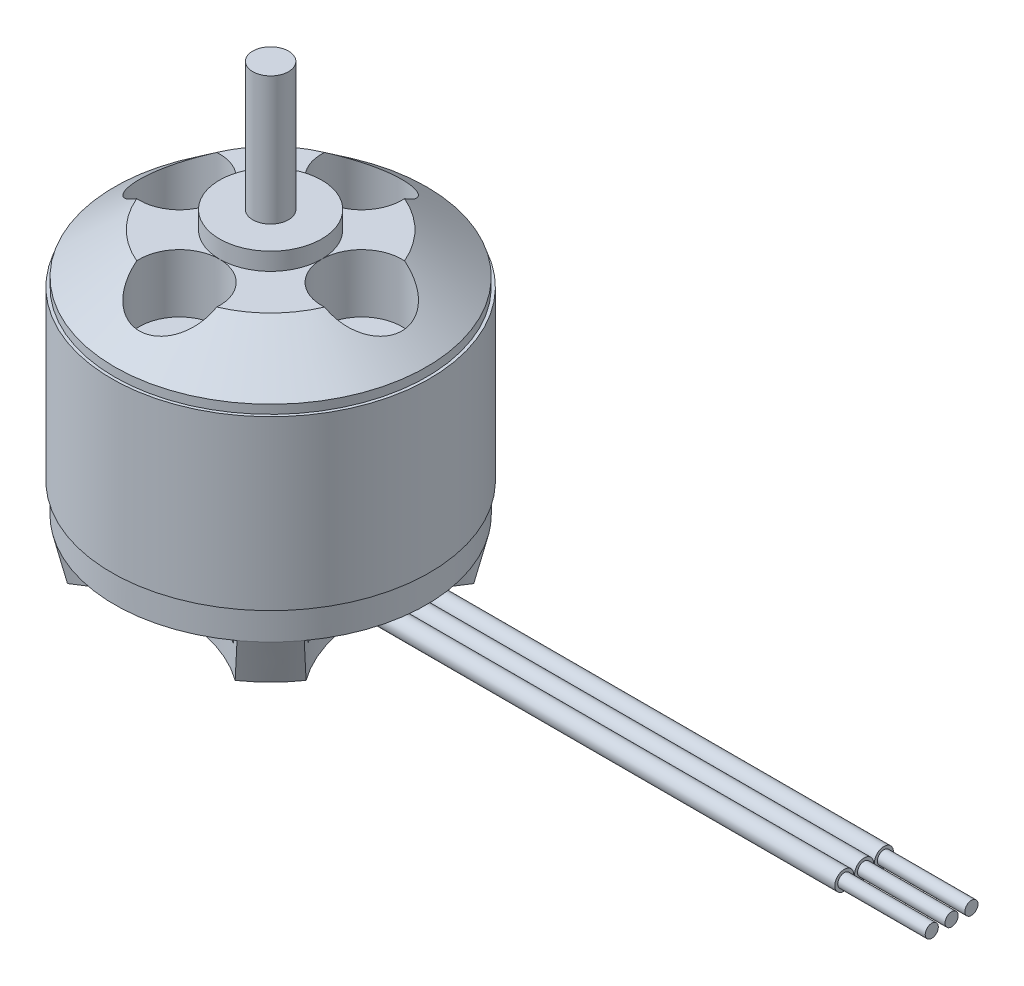
SolidWorks part; units mm, degrees
material "Plain Carbon Steel"
ref_plane "Front" through (0, 0, 0) normal (0, 0, 1) x (1, 0, 0)
ref_plane "Top" through (0, 0, 0) normal (0, 1, 0) x (1, 0, 0)
ref_plane "Right" through (0, 0, 0) normal (1, 0, 0) x (0, 0, -1)
sketch "Sketch1" plane through (0, 0, 0) normal (0, 0, 1) x (1, 0, 0)
  line L0 (0, 11.176) -> (1.5558, 11.176)
  line L1 (0, -50) -> (0, 50) construction
  line L2 (1.5558, 11.176) -> (1.5558, 0)
  line L3 (50, 0) -> (-50, 0) construction
  line L4 (1.5558, 0) -> (4.445, 0)
  line L5 (4.445, 0) -> (4.445, -1.524)
  line L6 (4.445, -1.524) -> (8.89, -1.524)
  line L7 (8.89, -1.524) -> (13.589, -5.08)
  line L8 (13.589, -5.08) -> (13.589, -5.842)
  line L9 (13.589, -5.842) -> (13.843, -5.842)
  line L10 (13.843, -5.842) -> (13.843, -20.4724)
  line L11 (13.589, -20.4724) -> (13.589, -23.0124)
  line L12 (13.589, -23.0124) -> (12.7, -26.67)
  line L13 (12.7, -26.67) -> (3.81, -26.67)
  line L14 (3.81, -26.67) -> (3.81, -26.924)
  line L15 (3.81, -26.924) -> (1.5558, -26.924)
  line L16 (1.5558, -26.924) -> (1.5558, -28.956)
  line L17 (1.5558, -28.956) -> (0, -28.956)
  line L18 (0, -28.956) -> (0, 11.176)
  line L19 (13.589, -20.4724) -> (13.843, -20.4724)
  dimension "D1" = 13.843
  dimension "D2" = 1.5557
  dimension "D3" = 11.176
  dimension "D4" = 4.445
  dimension "D5" = 1.524
  dimension "D6" = 8.89
  dimension "D7" = 4.318
  dimension "D8" = 0.762
  dimension "D9" = 0.254
  dimension "D10" = 14.6304
  dimension "D11" = 2.54
  dimension "D12" = 25.146
  dimension "D13" = 12.7
  dimension "D14" = 3.81
  dimension "D15" = 0.254
  dimension "D16" = 40.132
revolve "Revolve1" add sketch "Sketch1" angle 360 about L18
sketch "Sketch2" plane through (0, -1.524, 0) normal (0, 1, 0) x (1, 0, 0)
  circle A0 centre (0, 7.9375) radius 3.4925
  circle A1 centre (7.9375, 0) radius 3.4925
  circle A2 centre (0, -7.9375) radius 3.4925
  circle A3 centre (-7.9375, 0) radius 3.4925
  circle A5 centre (0, 0) radius 4.445 construction
  circle A7 centre (0, 0) radius 4.445 construction
  dimension "D2" = 6.985
extrude "Cut-Extrude1" cut sketch "Sketch2" against normal blind 5.08
sketch "Sketch3" plane through (0, -26.67, 0) normal (0, -1, 0) x (1, 0, 0)
  line L1 (-7.3025, 10.3905) -> (7.3025, 10.3905) construction
  circle A0 centre (0, 20.4866) radius 12.4602
  circle A1 centre (-20.4866, 0) radius 12.4602
  circle A2 centre (0, -20.4866) radius 12.4602
  circle A3 centre (20.4866, 0) radius 12.4602
  circle A4 centre (0, 0) radius 8.0264 construction
  circle A5 centre (0, 0) radius 12.7 construction
  dimension "D1" = 16.0528
  dimension "D2" = 14.605
extrude "Cut-Extrude2" cut sketch "Sketch3" against normal offset from surface (3.6576 mm away) 2.54 up to face at (0, -20.4724, -13.843)
sketch "Sketch4" plane through (0, -23.0124, 0) normal (0, -1, 0) x (1, 0, 0)
  circle A0 centre (0, 0) radius 12.1158
  arc A2 (8.0324, 10.9609) -> (-8.0324, 10.9609) centre (0, 0) ccw construction
  dimension "D1" = 1.4732
extrude "Cut-Extrude3" cut sketch "Sketch4" against normal blind 2.54 and the other way blind 1.27
hole_wizard "#4-40 Tapped Hole1" positions "Sketch7" profile "Sketch6" tap size "#4-40" standard "ANSI Inch"
sketch "Sketch7" plane through (0, -26.67, 0) normal (0, -1, 0) x (-1, 0, 0)
  line L0 (6.6723, 6.6723) -> (-6.6723, -6.6723) construction
  line L2 (5.6665, -5.6665) -> (-5.6665, 5.6665) construction
  line L5 (0, 0) -> (0, -19.5936) construction
  point P16 (5.6665, -5.6665)
  point P18 (-6.6723, -6.6723)
  point P20 (-5.6665, 5.6665)
  point P22 (6.6723, 6.6723)
  dimension "D1" = 18.8722
  dimension "D2" = 16.0274
  dimension "D3" = 45
sketch "Sketch6" plane through (-5.6665, -26.67, 5.6665) normal (1, 0, 0) x (0, 0, -1)
  line L0 (0, 0) -> (0, 3.2192)
  line L1 (0, 3.2192) -> (1.1303, 2.54)
  line L2 (1.1303, 2.54) -> (1.1303, 0.3937)
  line L3 (1.1303, 0.3937) -> (1.524, 0)
  line L5 (1.524, 0) -> (0, 0)
  line L6 (-1.1303, 0.3937) -> (-1.524, 0) construction
  line L10 (0, 3.2192) -> (-1.1303, 2.54) construction
  line L11 (0, -6.35) -> (0, 107.95) construction
  dimension "Tap Drill Dia." = 2.2606
  dimension "Tap Drill Depth" = 2.54
  dimension "Near C'Sink Dia." = 3.048
  dimension "Near C'Sink Angle" = 90
  dimension "Drill Angle" = 118
cosmetic thread "Hole Thread7" parameters "D1"=2.0853, "D2"=2.8448
cosmetic thread "Hole Thread8" parameters "D1"=2.0853, "D2"=2.8448
cosmetic thread "Hole Thread9" parameters "D1"=2.0853, "D2"=2.8448
cosmetic thread "Hole Thread10" parameters "D1"=2.0853, "D2"=2.8448
sketch "Sketch10" plane through (0, 0, 0) normal (1, 0, 0) x (0, 0, -1)
  line L1 (-12.1158, -20.4724) -> (12.1158, -20.4724) construction
  line L2 (-1.7272, -21.2979) -> (0, -21.2979) construction
  line L3 (0, -21.2979) -> (1.7272, -21.2979) construction
  circle A0 centre (0, -21.2979) radius 0.8255
  circle A1 centre (-1.7272, -21.2979) radius 0.8255
  circle A2 centre (1.7272, -21.2979) radius 0.8255
  dimension "D1" = 1.651
  dimension "D2" = 1.7272
sketch "Sketch12" plane through (0, 0, 0) normal (0, 0, 1) x (1, 0, 0)
  line L0 (0, -21.2979) -> (3.81, -21.2979)
  line L1 (0, -22.1234) -> (0, -20.4724) construction
  line L2 (9.5697, -23.8815) -> (51.689, -23.8815)
  line L3 (-13.843, -20.4724) -> (13.843, -20.4724) construction
  line L4 (-13.843, -20.4724) -> (13.589, -20.4724) construction
  line L5 (13.589, -23.0124) -> (13.589, -20.4724) construction
  arc A0 (3.81, -21.2979) -> (6.6898, -22.5897) centre (3.81, -25.1539) cw
  arc A1 (6.6898, -22.5897) -> (9.5697, -23.8815) centre (9.5697, -20.0255) ccw
  dimension "D1" = 2.5836
  dimension "D2" = 38.1
  dimension "D3" = 3.81
sweep "Sweep1" add profiles "Sketch10" path "Sketch12"
sketch "Sketch13" plane through (51.689, 0, 0) normal (1, 0, 0) x (0, 0, -1)
  circle A0 centre (1.7272, -23.8815) radius 0.8255 construction
  circle A1 centre (0, -23.8815) radius 0.8255 construction
  circle A2 centre (-1.7272, -23.8815) radius 0.8255 construction
  circle A3 centre (1.7272, -23.8815) radius 0.8255 construction
  circle A4 centre (0, -23.8815) radius 0.8255 construction
  circle A5 centre (-1.7272, -23.8815) radius 0.8255 construction
  circle A6 centre (1.7272, -23.8815) radius 0.5715
  circle A7 centre (0, -23.8815) radius 0.5715
  circle A8 centre (-1.7272, -23.8815) radius 0.5715
  dimension "D1" = 0.254
extrude "Boss-Extrude1" add sketch "Sketch13" along normal blind 7.62
